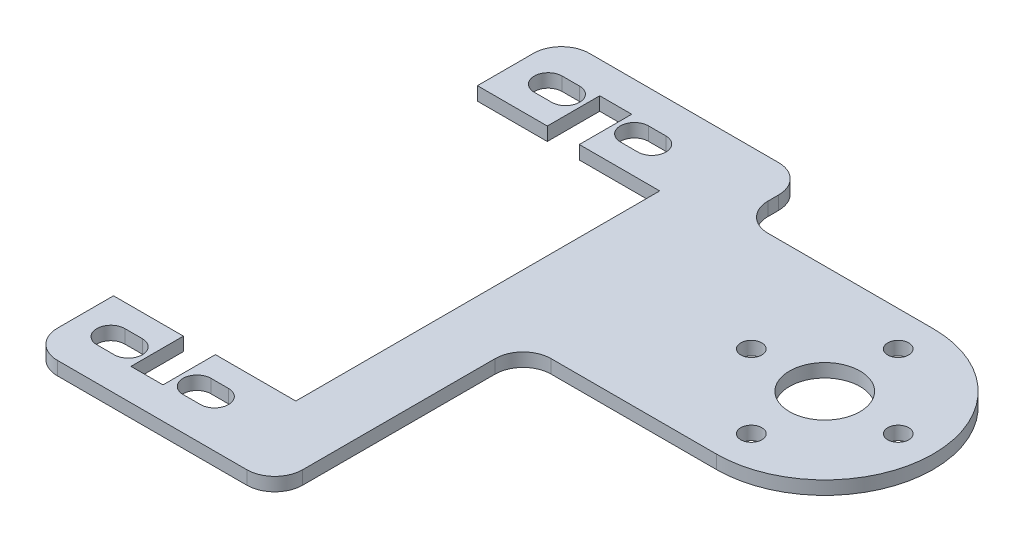
SolidWorks part; units mm, degrees
ref_plane "Front" through (0, 0, 0) normal (0, 0, 1) x (1, 0, 0)
ref_plane "Top" through (0, 0, 0) normal (0, 1, 0) x (1, 0, 0)
ref_plane "Right" through (0, 0, 0) normal (1, 0, 0) x (0, 0, -1)
sketch "Sketch1" plane through (0, 0, 0) normal (0, 1, 0) x (1, 0, 0)
  line L0 (0, 3.175) -> (0, 9.525)
  line L1 (3.175, 60.325) -> (24.638, 60.325)
  line L2 (3.175, 0) -> (24.638, 0)
  line L3 (27.813, 3.175) -> (27.813, 24.9936)
  line L4 (0, 50.8) -> (0, 57.15)
  line L5 (30.988, 28.1686) -> (49.7205, 28.1686)
  line L6 (49.7205, 52.7812) -> (30.988, 52.7812)
  line L7 (27.813, 55.9562) -> (27.813, 57.15)
  line L10 (0, 9.525) -> (7.9248, 9.525)
  line L11 (20.6756, 9.525) -> (20.6756, 50.8)
  line L14 (11.557, 9.525) -> (20.6756, 9.525)
  line L15 (7.9248, 9.525) -> (7.9248, 3.5814)
  line L16 (5.842, 53.3781) -> (3.8608, 53.3781)
  line L17 (11.557, 9.525) -> (11.557, 3.5814)
  line L18 (11.557, 3.5814) -> (7.9248, 3.5814)
  line L20 (13.6398, 6.9469) -> (15.621, 6.9469)
  line L21 (3.8608, 56.5531) -> (5.842, 56.5531)
  line L22 (15.621, 3.7719) -> (13.6398, 3.7719)
  line L23 (3.8608, 3.7719) -> (5.842, 3.7719)
  line L24 (15.621, 56.5531) -> (13.6398, 56.5531)
  line L25 (5.842, 6.9469) -> (3.8608, 6.9469)
  line L26 (13.6398, 53.3781) -> (15.621, 53.3781)
  line L27 (11.557, 56.7436) -> (7.9248, 56.7436)
  line L28 (11.557, 50.8) -> (11.557, 56.7436)
  line L29 (7.9248, 50.8) -> (7.9248, 56.7436)
  line L30 (11.557, 50.8) -> (20.6756, 50.8)
  line L31 (0, 50.8) -> (7.9248, 50.8)
  arc A0 (49.7205, 28.1686) -> (49.7205, 52.7812) centre (49.7205, 40.4749) ccw
  arc A1 (3.8608, 6.9469) -> (3.8608, 3.7719) centre (3.8608, 5.3594) ccw
  arc A2 (13.6398, 3.7719) -> (13.6398, 6.9469) centre (13.6398, 5.3594) cw
  arc A3 (5.842, 3.7719) -> (5.842, 6.9469) centre (5.842, 5.3594) ccw
  arc A4 (15.621, 6.9469) -> (15.621, 3.7719) centre (15.621, 5.3594) cw
  arc A5 (15.621, 53.3781) -> (15.621, 56.5531) centre (15.621, 54.9656) ccw
  arc A6 (5.842, 56.5531) -> (5.842, 53.3781) centre (5.842, 54.9656) cw
  arc A7 (13.6398, 56.5531) -> (13.6398, 53.3781) centre (13.6398, 54.9656) ccw
  arc A8 (3.8608, 53.3781) -> (3.8608, 56.5531) centre (3.8608, 54.9656) cw
  arc A9 (3.175, 60.325) -> (0, 57.15) centre (3.175, 57.15) ccw
  arc A10 (27.813, 57.15) -> (24.638, 60.325) centre (24.638, 57.15) ccw
  arc A11 (30.988, 52.7812) -> (27.813, 55.9562) centre (30.988, 55.9562) cw
  arc A12 (27.813, 24.9936) -> (30.988, 28.1686) centre (30.988, 24.9936) cw
  arc A13 (24.638, 0) -> (27.813, 3.175) centre (24.638, 3.175) ccw
  arc A14 (0, 3.175) -> (3.175, 0) centre (3.175, 3.175) ccw
  circle A16 centre (49.7205, 40.4749) radius 4.0005
  circle A17 centre (41.3893, 40.4749) radius 1.1938
  circle A18 centre (49.7205, 32.1437) radius 1.1938
  circle A19 centre (58.0517, 40.4749) radius 1.1938
  circle A20 centre (49.7205, 48.8061) radius 1.1938
  point P35 (4.8514, 5.3594)
  point P40 (4.8514, 5.3594)
  point P42 (14.6304, 5.3594)
  point P59 (14.6304, 54.9656)
  point P60 (4.8514, 54.9656)
extrude "Extrude1" add sketch "Sketch1" along normal blind 1.524
